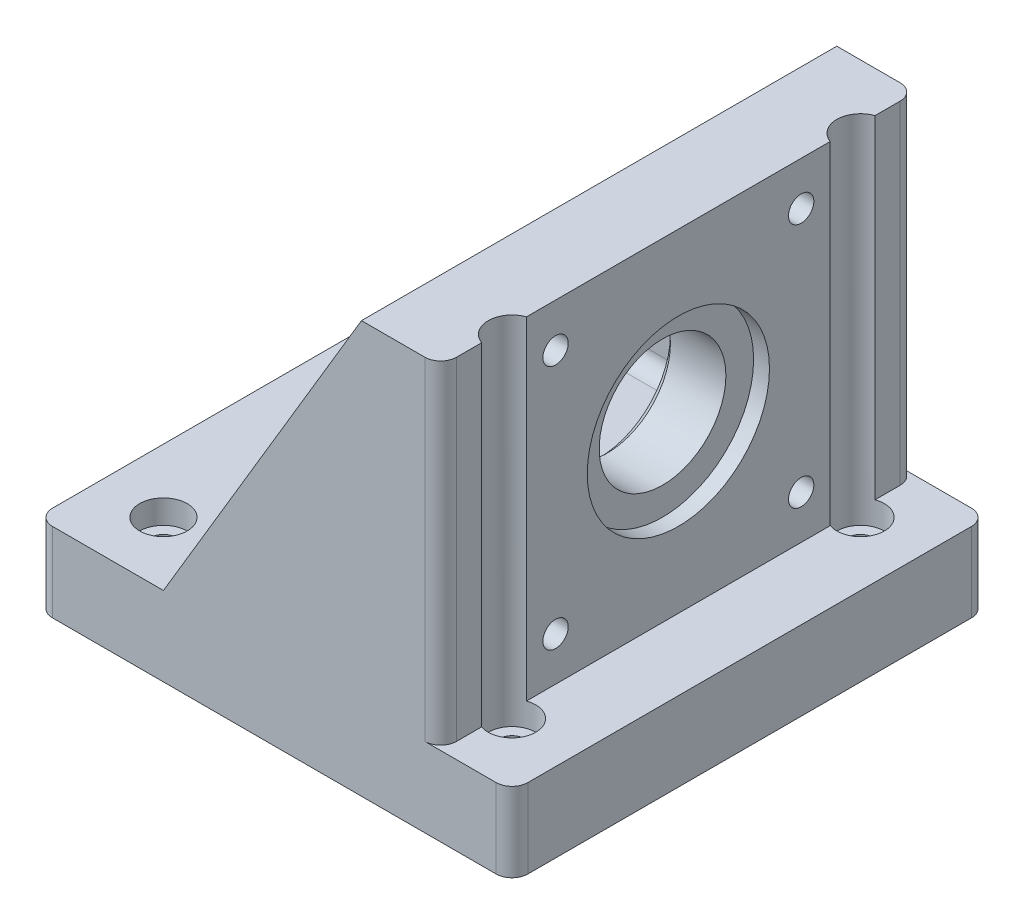
SolidWorks part; units mm, degrees
ref_plane "Front Plane" through (0, 0, 0) normal (0, 0, 1) x (1, 0, 0)
ref_plane "Top Plane" through (0, 0, 0) normal (0, 1, 0) x (1, 0, 0)
ref_plane "Right Plane" through (0, 0, 0) normal (1, 0, 0) x (0, 0, -1)
sketch "Sketch1" plane through (0, 0, 0) normal (0, 1, 0) x (1, 0, 0)
  line L0 (0, 24.3124) -> (0, 12.6406) construction
  line L1 (-30, 30) -> (30, 30)
  line L2 (-30, 30) -> (-30, -30)
  line L3 (-30, -30) -> (30, -30)
  line L4 (30, 30) -> (30, -30)
  line L5 (-30, 30) -> (30, -30) construction
  line L6 (-30, -30) -> (30, 30) construction
  line L7 (-6, 11) -> (6, 11)
  line L8 (-6, 11) -> (-6, -11)
  line L9 (-6, -11) -> (6, -11)
  line L10 (6, 11) -> (6, -11)
  line L11 (-6, 11) -> (6, -11) construction
  line L12 (-6, -11) -> (6, 11) construction
  line L13 (-22.8694, 0) -> (-9.755, 0) construction
  circle A0 centre (-22, 22) radius 1.6
  circle A1 centre (22, 22) radius 1.6
  circle A2 centre (-22, -22) radius 1.6
  circle A3 centre (22, -22) radius 1.6
  point P0 (0, 0)
  point P6 (0, 0)
  dimension "D7" = 3.2
  dimension "D1" = 60
  dimension "D2" = 60
  dimension "D3" = 12
  dimension "D4" = 22
  dimension "D5" = 8
  dimension "D6" = 8
extrude "Boss-Extrude1" add sketch "Sketch1" along normal blind 10
sketch "Sketch2" plane through (0, 10, 0) normal (0, 1, 0) x (1, 0, 0)
  line L1 (11, 30) -> (21, 30)
  line L2 (11, 25) -> (11, -25)
  line L3 (11, -30) -> (21, -30)
  line L4 (21, 30) -> (21, -30)
  line L5 (11, 30) -> (21, -30) construction
  line L6 (11, -30) -> (21, 30) construction
  line L7 (11, 30) -> (-14, 30)
  line L9 (11, 25) -> (-14, 25)
  line L10 (-14, 30) -> (-14, 25)
  line L11 (11, -30) -> (-14, -30)
  line L13 (11, -25) -> (-14, -25)
  line L14 (-14, -30) -> (-14, -25)
  point P0 (16, 0)
  dimension "D1" = 10
  dimension "D2" = 60
  dimension "D3" = 16
  dimension "D4" = 25
  dimension "D5" = 5
  dimension "D6" = 5
extrude "Boss-Extrude2" add sketch "Sketch2" along normal blind 42
sketch "Sketch3" plane through (21, 0, 0) normal (1, 0, 0) x (0, 0, -1)
  circle A0 centre (0, 31) radius 11.5
  dimension "D1" = 23
extrude "Cut-Extrude1" cut sketch "Sketch3" against normal blind 2
sketch "Sketch4" plane through (19, 0, 0) normal (1, 0, 0) x (0, 0, -1)
  circle A0 centre (0, 31) radius 8
  dimension "D1" = 16
extrude "Cut-Extrude2" cut sketch "Sketch4" against normal up to surface (8 mm away) up to face at (11, 31, 0)
sketch "Sketch5" plane through (21, 0, 0) normal (1, 0, 0) x (0, 0, -1)
  line L0 (0, 49.2207) -> (0, 43.7793) construction
  line L1 (-15.5, 46.5) -> (15.5, 46.5) construction
  line L2 (-15.5, 46.5) -> (-15.5, 15.5) construction
  line L3 (-15.5, 15.5) -> (15.5, 15.5) construction
  line L4 (15.5, 46.5) -> (15.5, 15.5) construction
  line L5 (-15.5, 46.5) -> (15.5, 15.5) construction
  line L6 (-15.5, 15.5) -> (15.5, 46.5) construction
  line L7 (-12.5576, 31) -> (-18.7197, 31) construction
  circle A0 centre (-15.5, 46.5) radius 1.6
  circle A1 centre (15.5, 46.5) radius 1.6
  circle A2 centre (15.5, 15.5) radius 1.6
  circle A3 centre (-15.5, 15.5) radius 1.6
  point P0 (0, 31)
  dimension "D3" = 3.2
  dimension "D1" = 31
  dimension "D2" = 31
extrude "Cut-Extrude3" cut sketch "Sketch5" against normal up to surface (10 mm away) up to face at (11, 31, -8)
sketch "Sketch6" plane through (0, 10, 0) normal (0, 1, 0) x (1, 0, 0)
  circle A0 centre (-22, 22) radius 3
  circle A1 centre (22, 22) radius 3
  circle A2 centre (22, -22) radius 3
  circle A3 centre (-22, -22) radius 3
  dimension "D1" = 6
  dimension "D2" = 6
  dimension "D3" = 6
  dimension "D4" = 6
extrude "Cut-Extrude4" cut sketch "Sketch6" against normal blind 3
sketch "Sketch7" plane through (0, 10, 0) normal (0, 1, 0) x (1, 0, 0)
  circle A0 centre (22, 22) radius 3
  circle A1 centre (22, -22) radius 3
extrude "Cut-Extrude5" cut sketch "Sketch7" along normal through all
sketch "Sketch10" plane through (0, 0, 0) normal (0, 0, 1) x (1, 0, 0)
  line L0 (11, 52) -> (-14, 10)
  line L1 (11, 10) -> (-14, 10) construction
  line L2 (-14, 52) -> (-14, 10) construction
  line L3 (-14, 10) -> (-19.68, 22.362)
  line L4 (-19.68, 22.362) -> (-19.68, 54.5845)
  line L5 (-19.68, 54.5845) -> (11, 54.5845)
  line L6 (11, 54.5845) -> (11, 52)
extrude "Cut-Extrude6" cut sketch "Sketch10" against normal through all both and the other way through all
fillet "Fillet1" radius 2 7 edges at (11, 31, 25) (11, 31, -25) (11, 10, 0) (-1.5, 10, 25) (-1.5, 10, -25) (21, 31, 30) (21, 31, -30)
fillet "Fillet2" radius 2 4 edges at (-30, 5, -30) (30, 5, -30) (30, 5, 30) (-30, 5, 30)
chamfer "Chamfer1" distance 1 angle 45 1 edges at (11, 31, -8)
